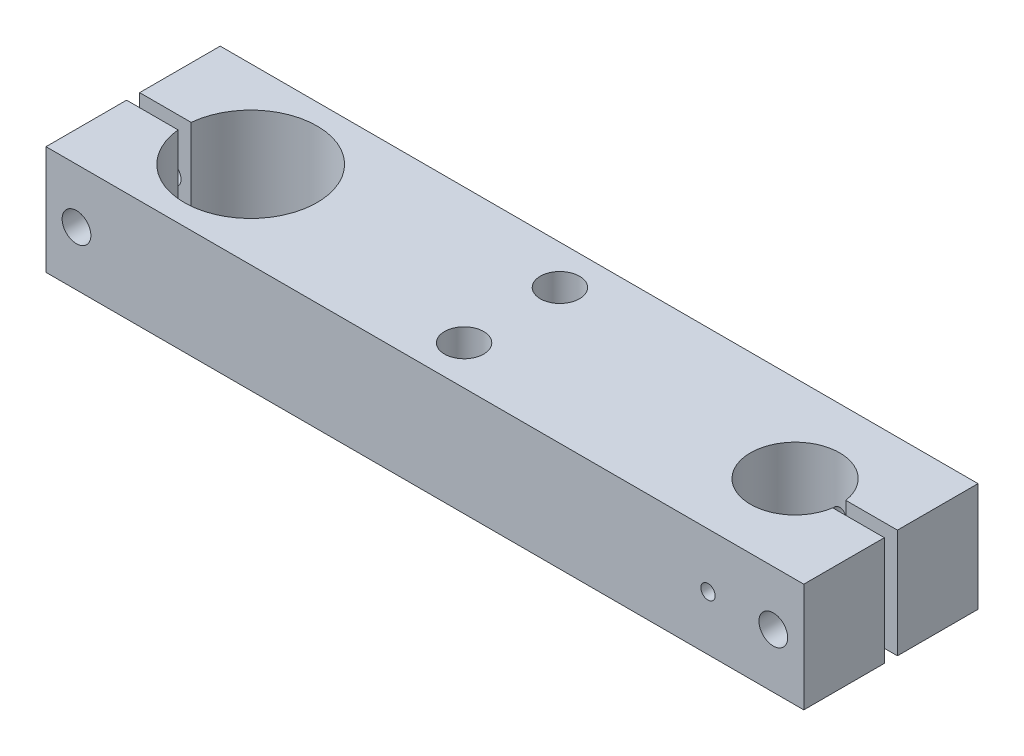
SolidWorks part; units mm, degrees
material "Acier non allié"
ref_plane "Plan de face" through (0, 0, 0) normal (0, 0, 1) x (1, 0, 0)
ref_plane "Plan de dessus" through (0, 0, 0) normal (0, 1, 0) x (1, 0, 0)
ref_plane "Plan de droite" through (0, 0, 0) normal (1, 0, 0) x (0, 0, -1)
sketch "Esquisse1" plane through (0, 0, 0) normal (0, 1, 0) x (1, 0, 0)
  line L0 (75.1396, 0) -> (0, 0) construction
  line L1 (-87, -20) -> (87, -20)
  line L2 (-87, -20) -> (-87, 20)
  line L3 (-87, 20) -> (87, 20)
  line L4 (87, -20) -> (87, 20)
  line L5 (-87, -20) -> (87, 20) construction
  line L6 (-87, 20) -> (87, -20) construction
  line L7 (87, 1.5) -> (75.1396, 1.5)
  line L8 (87, 1.5) -> (87, -1.5)
  line L9 (87, -1.5) -> (75.1396, -1.5)
  line L10 (75.1396, 1.5) -> (75.1396, -1.5)
  line L11 (-70.0245, 0) -> (0, 0) construction
  line L12 (-87, 1.5) -> (-70.0245, 1.5)
  line L13 (-87, 1.5) -> (-87, -1.5)
  line L14 (-87, -1.5) -> (-70.0245, -1.5)
  line L15 (-70.0245, 1.5) -> (-70.0245, -1.5)
  circle A0 centre (65, 0) radius 10.25
  circle A1 centre (-60, 0) radius 15.25
  point P0 (0, 0)
  point P16 (-44.75, 0)
  point P22 (-70.0245, 6.194)
  point P25 (-59.9614, -1.4211)
  dimension "D1" = 20.5
  dimension "D6" = 30.5
  dimension "D2" = 40
  dimension "D3" = 3
  dimension "D4" = 22
  dimension "D5" = 125
  dimension "D7" = 27
  dimension "D8" = 3
extrude "Boss.-Extru.1" add sketch "Esquisse1" along normal blind 25 contours A0 L7 L4 L3 L2 L1 L9
sketch "Esquisse2" plane through (0, 0, 20) normal (0, 0, 1) x (1, 0, 0)
  line L1 (80, 12.5) -> (87, 12.5) construction
  line L3 (87, 25) -> (87, 0) construction
  line L4 (-87, 25) -> (-87, 0) construction
  point P0 (80, 12.5)
  point P4 (-80, 12.5)
  point P5 (0, 0)
  dimension "D1" = 7
  dimension "D3" = 7
hole_wizard "Dégagement M61" positions "Esquisse3D2" profile "Esquisse4" hole size "M6" standard "ISO" end condition up to next
sketch3d "Esquisse3D2"
  point P0 (80, 12.5, 20)
  point P9 (80, 12.5, 20)
  point P10 (-80, 12.5, 20)
sketch "Esquisse4" plane through (80, 12.5, 20) normal (1, 0, 0) x (0, -1, 0)
  line L0 (0, 0) -> (0, 18.5)
  line L1 (0, 18.5) -> (3.3, 18.5)
  line L2 (3.3, 18.5) -> (3.3, 0)
  line L5 (3.3, 0) -> (0, 0)
  line L11 (0, -6.35) -> (0, 107.95) construction
  dimension "Diamètre du perçage jusqu'au prochain" = 6.6
  dimension "Profondeur du perçage jusqu'au prochain" = 18.5
sketch "Esquisse5" plane through (0, 0, -1.5) normal (0, 0, 1) x (1, 0, 0)
  point P0 (-80, 12.5)
  point P2 (80, 12.5)
  point P4 (0, 0)
  point P6 (0, 0)
hole_wizard "Trou taraudé M61" positions "Esquisse3D3" profile "Esquisse6" tap size "M6" standard "ISO" end condition through all
sketch3d "Esquisse3D3"
  point P0 (80, 12.5, -1.5)
  point P8 (80, 12.5, -1.5)
  point P11 (-80, 12.5, -1.5)
sketch "Esquisse6" plane through (80, 12.5, -1.5) normal (1, 0, 0) x (0, -1, 0)
  line L0 (0, 0) -> (0, 18.5)
  line L1 (0, 18.5) -> (2.5, 18.5)
  line L2 (2.5, 18.5) -> (2.5, 0)
  line L5 (2.5, 0) -> (0, 0)
  line L11 (0, -6.35) -> (0, 107.95) construction
  dimension "Diamètre du trou pour taraudage jusqu'au prochain" = 5
  dimension "Profondeur du trou pour taraudage jusqu'au prochain" = 18.5
cosmetic thread "Filetage de perçage4" parameters "D2"=6
cosmetic thread "Filetage de perçage5" parameters "D2"=6
cosmetic thread "Filetage de perçage6" parameters "D2"=6
sketch "Esquisse7" plane through (0, 0, 20) normal (0, 0, 1) x (1, 0, 0)
  line L0 (75.1396, 25) -> (54.75, 25) construction
  line L1 (75.1396, 25) -> (54.75, 25)
  line L2 (65, 25) -> (65, 12.5) construction
  line L3 (65, 12.5) -> (87, 12.5) construction
  line L4 (87, 25) -> (87, 0) construction
  point P2 (65, 12.5)
  point P5 (0, 0)
  dimension "D1" = 22
hole_wizard "Trou taraudé M41" positions "Esquisse3D4" profile "Esquisse8" tap size "M4" standard "ISO" end condition through all
sketch3d "Esquisse3D4"
  line L0 (75.1396, 25, 20) -> (54.75, 25, 20) construction
  line L1 (75.1396, 25, 20) -> (54.75, 25, 20)
  point P6 (65, 12.5, 20)
  point P10 (65, 12.5, 20)
sketch "Esquisse8" plane through (65, 12.5, 20) normal (1, 0, 0) x (0, -1, 0)
  line L0 (0, 0) -> (0, 40)
  line L1 (0, 40) -> (1.65, 40)
  line L2 (1.65, 40) -> (1.65, 0)
  line L5 (1.65, 0) -> (0, 0)
  line L11 (0, -6.35) -> (0, 107.95) construction
  dimension "Diamètre du trou pour taraudage jusqu'au prochain" = 3.3
  dimension "Profondeur du trou pour taraudage jusqu'au prochain" = 40
cosmetic thread "Filetage de perçage3" parameters "D2"=4
cosmetic thread "Filetage de perçage7" parameters "D2"=4
sketch "Esquisse10" plane through (0, 25, 0) normal (0, 1, 0) x (1, 0, 0)
  point P0 (0, 11)
  point P1 (0, -11)
  point P2 (0, 0)
  point P6 (-2.8618, 0.4266)
  dimension "D1" = 11
  dimension "D2" = 11
hole_wizard "Dégagement M81" positions "Esquisse3D5" profile "Esquisse11" hole size "M8" standard "ISO" end condition through all
sketch3d "Esquisse3D5"
  point P0 (0, 25, -11)
  point P3 (0, 25, 11)
sketch "Esquisse11" plane through (0, 25, -11) normal (1, 0, 0) x (0, 0, 1)
  line L0 (0, 0) -> (0, 25)
  line L1 (0, 25) -> (4.5, 25)
  line L2 (4.5, 25) -> (4.5, 0)
  line L5 (4.5, 0) -> (0, 0)
  line L11 (0, -6.35) -> (0, 107.95) construction
  dimension "Diamètre du perçage jusqu'au prochain" = 9
  dimension "Profondeur du perçage jusqu'au prochain" = 25
